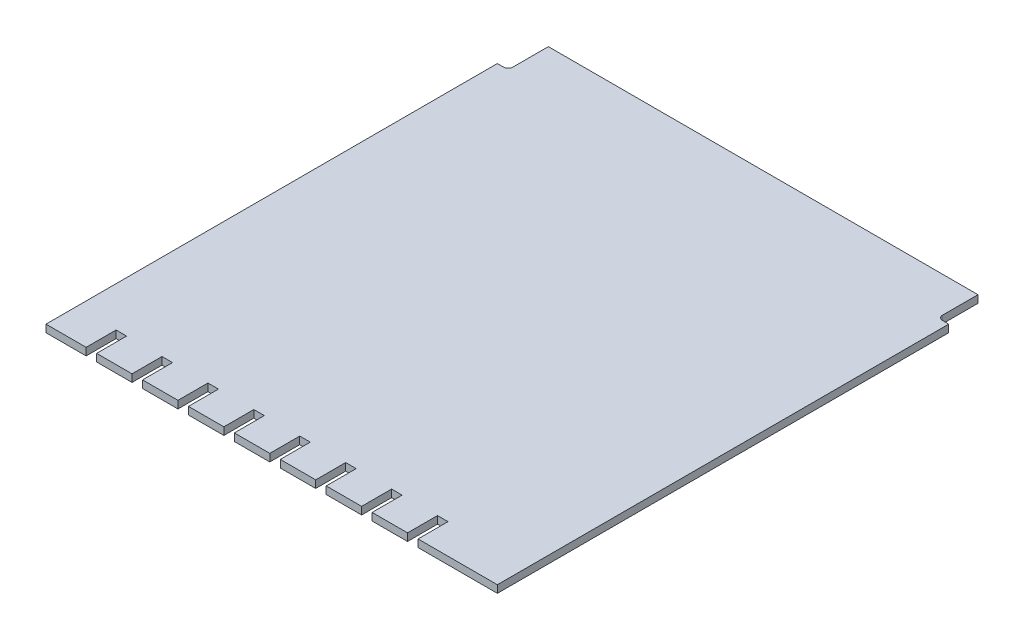
SolidWorks part; units mm, degrees
ref_plane "Front Plane" through (0, 0, 0) normal (0, 0, 1) x (1, 0, 0)
ref_plane "Top Plane" through (0, 0, 0) normal (0, 1, 0) x (1, 0, 0)
ref_plane "Right Plane" through (0, 0, 0) normal (1, 0, 0) x (0, 0, -1)
sketch "Sketch1" plane through (0, 0, 0) normal (0, 1, 0) x (1, 0, 0)
  line L0 (4.5, 96.6) -> (4.5, 104.1)
  line L1 (2.2, 0) -> (97.8, 0) construction
  line L2 (4.5, 104.1) -> (95.5, 104.1)
  line L3 (2.2, 95.6) -> (97.8, 95.6) construction
  line L4 (95.5, 104.1) -> (95.5, 96.6)
  line L5 (2.2, 95.6) -> (3.5, 95.6)
  line L6 (96.5, 95.6) -> (97.8, 95.6)
  line L7 (10.7, 0) -> (10.7, 6.3449)
  line L8 (10.7, 6.3449) -> (12.925, 6.3449)
  line L9 (12.925, 6.3449) -> (12.925, 0)
  line L10 (12.925, 0) -> (20.425, 0)
  line L11 (20.425, 0) -> (20.425, 6.3449)
  line L12 (20.425, 6.3449) -> (22.65, 6.3449)
  line L13 (22.65, 6.3449) -> (22.65, 0)
  line L14 (22.65, 0) -> (30.15, 0)
  line L15 (30.15, 0) -> (30.15, 6.3449)
  line L16 (2.2, 0) -> (2.2, 95.6)
  line L17 (30.15, 6.3449) -> (32.375, 6.3449)
  line L18 (97.8, 0) -> (97.8, 95.6)
  line L19 (32.375, 6.3449) -> (32.375, 0)
  line L20 (32.375, 0) -> (39.875, 0)
  line L21 (2.2, 0) -> (10.7, 0)
  line L22 (39.875, 0) -> (39.875, 6.3449)
  line L23 (39.875, 6.3449) -> (42.1, 6.3449)
  line L24 (42.1, 6.3449) -> (42.1, 0)
  line L25 (42.1, 0) -> (49.6, 0)
  line L26 (49.6, 0) -> (49.6, 6.3449)
  line L27 (49.6, 6.3449) -> (51.825, 6.3449)
  line L28 (51.825, 6.3449) -> (51.825, 0)
  line L29 (51.825, 0) -> (59.325, 0)
  line L30 (59.325, 0) -> (59.325, 6.3449)
  line L31 (59.325, 6.3449) -> (61.55, 6.3449)
  line L32 (61.55, 6.3449) -> (61.55, 0)
  line L33 (61.55, 0) -> (69.05, 0)
  line L34 (69.05, 0) -> (69.05, 6.3449)
  line L35 (69.05, 6.3449) -> (71.275, 6.3449)
  line L36 (71.275, 6.3449) -> (71.275, 0)
  line L37 (71.275, 0) -> (78.775, 0)
  line L38 (78.775, 0) -> (78.775, 6.3449)
  line L39 (78.775, 6.3449) -> (81, 6.3449)
  line L40 (81, 6.3449) -> (81, 0)
  line L41 (81, 0) -> (97.8, 0)
  arc A0 (95.5, 96.6) -> (96.5, 95.6) centre (96.5, 96.6) ccw
  arc A1 (4.5, 96.6) -> (3.5, 95.6) centre (3.5, 96.6) cw
  point P8 (95.5, 95.6)
  point P11 (4.5, 95.6)
  dimension "D1" = 1
extrude "Boss-Extrude1" add sketch "Sketch1" along normal blind 1.5875
ref_plane "center-of-slot" through (0, 0.7937, 0) normal (0, 1, 0) x (1, 0, 0)
ref_plane "Plane1" through (50, 0, 0) normal (-1, 0, 0) x (0, 0, 1)
